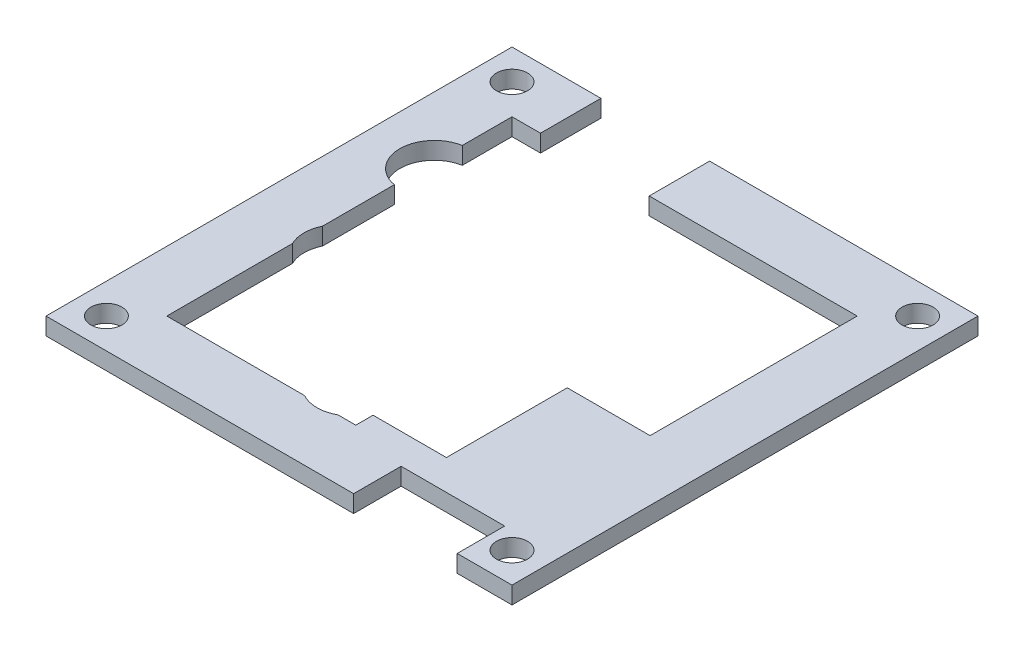
SolidWorks part; units mm, degrees
ref_plane "Front" through (0, 0, 0) normal (0, 0, 1) x (1, 0, 0)
ref_plane "Top" through (0, 0, 0) normal (0, 1, 0) x (1, 0, 0)
ref_plane "Right" through (0, 0, 0) normal (1, 0, 0) x (0, 0, -1)
sketch "草图3" plane through (0, 0, 0) normal (0, 1, 0) x (1, 0, 0)
  line L0 (16.9, -20) -> (20, -20)
  line L1 (-20, -20) -> (12.4, -20)
  line L2 (20, -20) -> (20, 20)
  line L3 (-27, 27) -> (-27, -27)
  line L4 (-27, -27) -> (27, -27)
  line L5 (27, -27) -> (27, 27)
  line L6 (27, 27) -> (-27, 27)
  line L7 (-8.6, 1.7) -> (-7.6812, 1.7)
  line L8 (-5.8437, 1.7) -> (-4.925, 1.7)
  line L9 (20.65, -20) -> (20, -20)
  line L10 (16.9, -6) -> (12.4, -6)
  line L11 (12.4, -6) -> (12.4, -19.5)
  line L12 (-10.4, 20) -> (-4.1, 20)
  line L13 (16.9, -6) -> (16.9, -19.5)
  line L14 (-20, 20) -> (-20, -20)
  line L15 (-3.0875, 1.7) -> (-2.1687, 1.7)
  line L16 (-0.3312, 1.7) -> (0.5875, 1.7)
  line L17 (2.425, 1.7) -> (3.3438, 1.7)
  line L18 (5.1813, 1.7) -> (6.1, 1.7)
  line L19 (8.8563, -13.3) -> (7.9375, -13.3)
  line L20 (8.65, -20) -> (8.65, -27)
  line L21 (-8.6, 1.7) -> (-8.6, -13.3)
  line L22 (-7.6812, -13.3) -> (-8.6, -13.3)
  line L23 (-8.6, -13.3) -> (-8.6029, -13.3589)
  line L24 (-10.4375, -13.3) -> (-11.3562, -13.3)
  line L25 (-10.4375, 1.7) -> (-11.3562, 1.7)
  line L26 (6.1, 1.7) -> (6.1, -13.3)
  line L27 (-4.925, -13.3) -> (-4.925, 1.7)
  line L28 (-11.3562, -13.3) -> (-11.3562, 1.7)
  line L29 (-3.0875, -13.3) -> (-3.0875, 1.7)
  line L30 (-10.4375, -13.3) -> (-10.4375, 1.7)
  line L31 (-2.1687, -13.3) -> (-2.1687, 1.7)
  line L32 (8.8563, 1.7) -> (7.9375, 1.7)
  line L33 (-5.8437, -13.3) -> (-5.8437, 1.7)
  line L34 (8.8563, -13.3) -> (8.8563, 1.7)
  line L35 (-7.6812, -13.3) -> (-7.6812, 1.7)
  line L36 (-0.3312, -13.3) -> (-0.3312, 1.7)
  line L37 (0.5875, -13.3) -> (0.5875, 1.7)
  line L38 (5.1813, -13.3) -> (6.1, -13.3)
  line L39 (2.425, -13.3) -> (2.425, 1.7)
  line L40 (3.3438, -13.3) -> (3.3438, 1.7)
  line L41 (2.425, -13.3) -> (3.3438, -13.3)
  line L42 (5.1813, -13.3) -> (5.1813, 1.7)
  line L43 (-0.3312, -13.3) -> (0.5875, -13.3)
  line L44 (-3.0875, -13.3) -> (-2.1687, -13.3)
  line L45 (-5.8437, -13.3) -> (-4.925, -13.3)
  line L46 (7.9375, -13.3) -> (7.9375, 1.7)
  line L47 (20.65, -20) -> (20.65, -27)
  line L48 (12.4, -19.5) -> (12.4, -20)
  line L49 (16.9, -19.5) -> (16.9, -20)
  line L50 (-20, -20) -> (20, -20) construction
  line L51 (-20, 20) -> (20, 20)
  line L52 (-16.7, 20) -> (-10.4, 20)
  line L53 (20, 20) -> (-20, 20) construction
  line L54 (-16.7, 20) -> (-16.7, 27)
  line L55 (-4.1, 20) -> (-4.1, 27)
  line L56 (12.4, -19.5) -> (16.9, -19.5)
  line L57 (1.9, -18) -> (12.4, -18)
  line L58 (8.65, -21.5) -> (20.65, -21.5)
  line L59 (1.9, -20) -> (1.9, -18)
  line L60 (16.9, -18) -> (16.1, -18)
  line L61 (16.9, -18) -> (20, -18)
  line L62 (12.4, -18) -> (13.4, -18)
  line L63 (13.4, -18) -> (13.4, -19.5)
  line L64 (16.1, -18) -> (16.1, -19.5)
  line L66 (10.4, -6) -> (10.4, -18)
  line L67 (10.4, -6) -> (10.4, -4)
  line L69 (10.4, -4) -> (20, -4)
  circle A0 centre (-23.5, -23.5) radius 1.8
  circle A1 centre (23.5, -23.5) radius 1.8
  circle A2 centre (-23.5, 23.5) radius 1.8
  circle A3 centre (23.5, 23.5) radius 1.8
  circle A4 centre (-2.1, -16.5) radius 2
  circle A5 centre (-16.4, -3.7) radius 2
  circle A6 centre (-19.3, 10.3) radius 2
  circle A7 centre (-1.1, 15.8) radius 2
  circle A8 centre (-19.3, 10.3) radius 4
  circle A9 centre (-2.1, -16.5) radius 4
  circle A10 centre (-1.1, 15.8) radius 4
  circle A11 centre (-16.4, -3.7) radius 4
  point P0 (0, 0)
  point P61 (-10.8969, 1.7)
  dimension "D1" = 7
extrude "凸台-拉伸2" add sketch "草图3" along normal blind 2 contours A11 L14 A8 L51 L54 L6 L3 L4 L20 L1 A9 A2 A0 | L55 L51 L2 L9 L47 L4 L5 L6 A3 A1 | L59 L1 L48 L11 L57 | L20 L58 L47 L9 L0 L49 L56 L48 L1 | L61 L13 L49 L0 L2 | L60 L64 L56 L13 | L63 L62 L11 L56 | L64 L60 L13 L10 L11 L62 L63 L56 | L69 L67 L66 L57 L11 L10 L13 L61 L2
